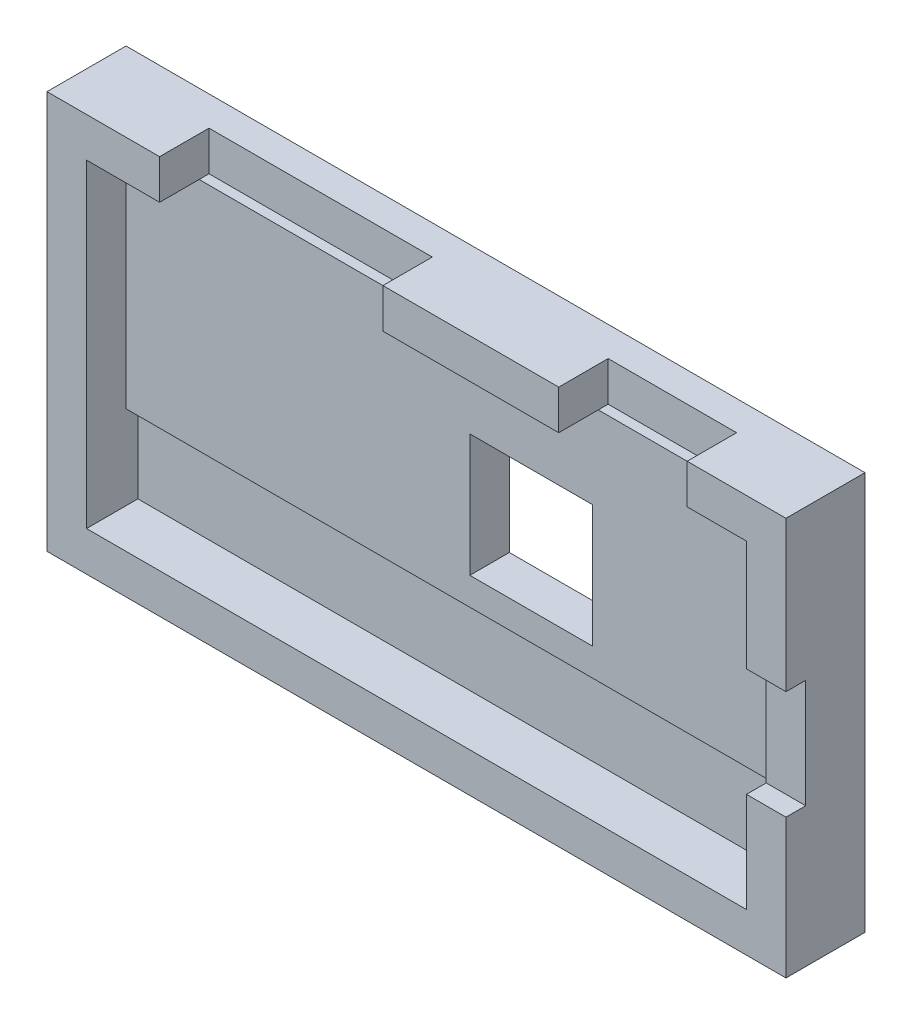
SolidWorks part; units mm, degrees
ref_plane "前基準面" through (0, 0, 0) normal (0, 0, 1) x (1, 0, 0)
ref_plane "上基準面" through (0, 0, 0) normal (0, 1, 0) x (1, 0, 0)
ref_plane "右基準面" through (0, 0, 0) normal (1, 0, 0) x (0, 0, -1)
sketch "草圖1" plane through (0, 0, 0) normal (0, 0, 1) x (1, 0, 0)
  line L1 (-34.3408, 16.0792) -> (32.4592, 16.0792)
  line L2 (-34.3408, 16.0792) -> (-34.3408, -16.2208)
  line L3 (-34.3408, -16.2208) -> (32.4592, -16.2208)
  line L4 (32.4592, 16.0792) -> (32.4592, -16.2208)
  line L5 (-38.3408, 20.0792) -> (36.4592, 20.0792)
  line L6 (-38.3408, 20.0792) -> (-38.3408, -20.2208)
  line L7 (-38.3408, -20.2208) -> (36.4592, -20.2208)
  line L8 (36.4592, 20.0792) -> (36.4592, -20.2208)
  dimension "D1" = 66.8
  dimension "D2" = 32.3
  dimension "D3" = 40.3
  dimension "D4" = 74.8
  dimension "D5" = 4
  dimension "D6" = 4
extrude "填料-伸長1" add sketch "草圖1" along normal blind 4 contours L5 L8 L7 L6
sketch "草圖2" plane through (0, 0, 4) normal (0, 0, 1) x (1, 0, 0)
  line L1 (-38.3408, 20.0792) -> (36.4592, 20.0792)
  line L2 (-38.3408, 20.0792) -> (-38.3408, -20.2208)
  line L3 (-38.3408, -20.2208) -> (36.4592, -20.2208)
  line L4 (36.4592, 20.0792) -> (36.4592, -20.2208)
  line L5 (-34.3408, 16.0792) -> (32.4592, 16.0792)
  line L6 (-34.3408, 16.0792) -> (-34.3408, -16.2208)
  line L7 (-34.3408, -16.2208) -> (32.4592, -16.2208)
  line L8 (32.4592, 16.0792) -> (32.4592, -16.2208)
  dimension "D1" = 4
  dimension "D2" = 4
  dimension "D3" = 66.8
  dimension "D4" = 32.3
extrude "伸長-薄件1" add sketch "草圖2" along normal blind 4 thin contours L6 L7 L8 L5
sketch "草圖3" plane through (0, 0, 0) normal (0, 0, -1) x (-1, 0, 0)
  line L0 (38.3408, 20.0792) -> (-36.4592, 20.0792) construction
  line L1 (-36.4592, 20.0792) -> (-36.4592, -20.2208) construction
  line L2 (38.3408, 20.0792) -> (38.3408, -20.2208) construction
  line L3 (38.3408, -20.2208) -> (-36.4592, -20.2208) construction
  circle A0 centre (-28.4592, 12.0792) radius 2.1255
  circle A1 centre (30.3408, 12.0792) radius 2.4168
  circle A2 centre (-28.4592, -12.2208) radius 2.076
  circle A3 centre (30.3408, -12.2208) radius 2.3736
  dimension "D4" = 8
  dimension "D6" = 8
  dimension "D7" = 8
  dimension "D8" = 8
  dimension "D1" = 8
  dimension "D2" = 8
  dimension "D3" = 8
  dimension "D5" = 8
extrude "填料-伸長2" add sketch "草圖3" along normal blind 1
sketch "草圖4" plane through (0, 0, 8) normal (0, 0, 1) x (1, 0, 0)
  line L0 (36.4592, 20.0792) -> (36.4592, -20.2208) construction
  line L1 (32.4592, 4.8792) -> (36.4592, 4.8792)
  line L2 (32.4592, 4.8792) -> (32.4592, -6.1208)
  line L3 (32.4592, -6.1208) -> (36.4592, -6.1208)
  line L4 (36.4592, 4.8792) -> (36.4592, -6.1208)
  dimension "D1" = 11.2
  dimension "D2" = 11
extrude "除料-伸長1" cut sketch "草圖4" against normal blind 2
sketch "草圖6" plane through (0, 0, 4) normal (0, 0, 1) x (1, 0, 0)
  line L0 (32.4592, 16.0792) -> (32.4592, -16.2208) construction
  line L1 (32.4592, -16.2208) -> (-34.3408, -16.2208)
  line L2 (32.4592, -16.2208) -> (32.4592, -7.7208)
  line L3 (32.4592, -7.7208) -> (-34.3408, -7.7208)
  line L4 (-34.3408, -16.2208) -> (-34.3408, -7.7208)
  line L5 (-34.3408, -16.2208) -> (32.4592, -16.2208) construction
  line L6 (-34.3408, 16.0792) -> (-34.3408, -16.2208) construction
  dimension "D1" = 8.5
extrude "除料-伸長3" cut sketch "草圖6" against normal blind 1.2
sketch "草圖7" plane through (0, 0, 8) normal (0, 0, 1) x (1, 0, 0)
  line L0 (-38.3408, 20.0792) -> (36.4592, 20.0792) construction
  line L1 (26.4592, 16.0792) -> (13.4592, 16.0792)
  line L2 (26.4592, 16.0792) -> (26.4592, 20.0792)
  line L3 (26.4592, 20.0792) -> (13.4592, 20.0792)
  line L4 (13.4592, 16.0792) -> (13.4592, 20.0792)
  line L7 (-34.3408, 16.0792) -> (32.4592, 16.0792) construction
  line L8 (-4.3408, 16.0792) -> (-26.9408, 16.0792)
  line L9 (-4.3408, 16.0792) -> (-4.3408, 20.0792)
  line L10 (-4.3408, 20.0792) -> (-26.9408, 20.0792)
  line L11 (-26.9408, 16.0792) -> (-26.9408, 20.0792)
  dimension "D1" = 13
  dimension "D2" = 6
  dimension "D3" = 17.8
  dimension "D5" = 7.4
extrude "除料-伸長4" cut sketch "草圖7" against normal blind 5
sketch "草圖9" plane through (0, 0, 4) normal (0, 0, 1) x (1, 0, 0)
  line L0 (32.4592, 16.0792) -> (32.4592, -7.7208) construction
  line L1 (12.8592, -4.9208) -> (0.4592, -4.9208)
  line L2 (12.8592, -4.9208) -> (12.8592, 7.4792)
  line L3 (12.8592, 7.4792) -> (0.4592, 7.4792)
  line L4 (0.4592, -4.9208) -> (0.4592, 7.4792)
  line L5 (-34.3408, 16.0792) -> (-26.9408, 16.0792) construction
  dimension "D1" = 19.6
  dimension "D2" = 8.6
  dimension "D3" = 12.4
  dimension "D4" = 12.4
extrude "除料-伸長5" cut sketch "草圖9" against normal up to next
